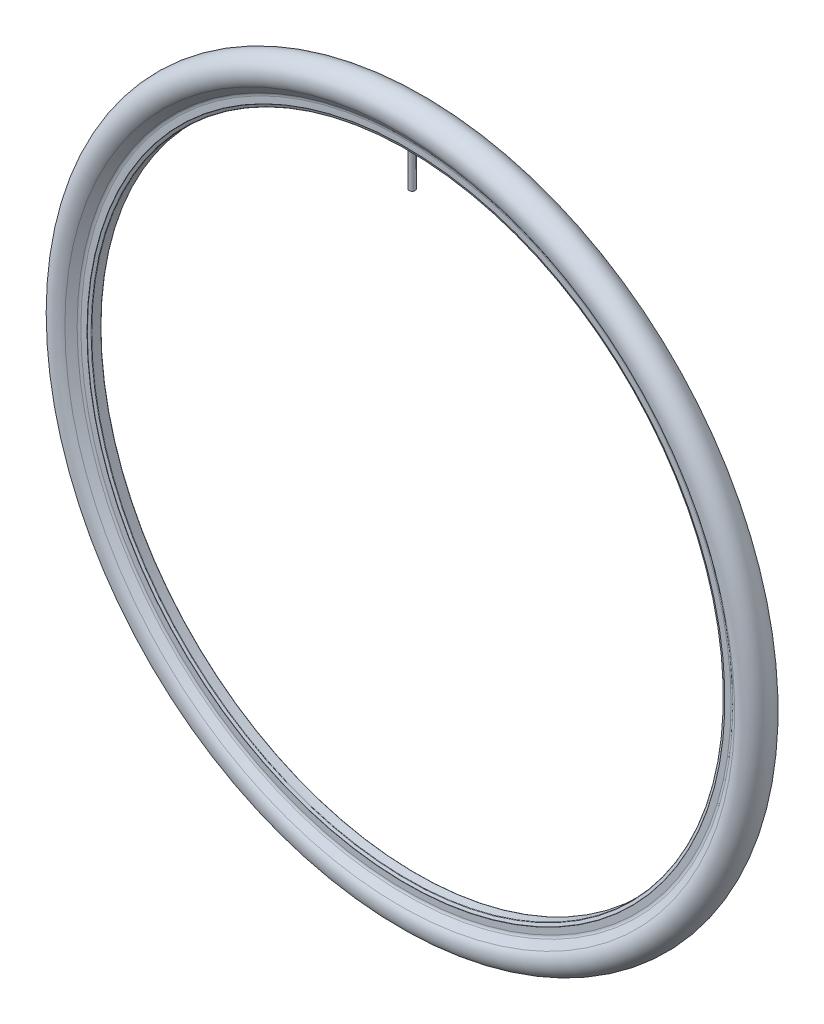
SolidWorks part; units mm, degrees
ref_plane "Plan de face" through (0, 0, 0) normal (0, 0, 1) x (1, 0, 0)
ref_plane "Plan de dessus" through (0, 0, 0) normal (0, 1, 0) x (1, 0, 0)
ref_plane "Plan de droite" through (0, 0, 0) normal (1, 0, 0) x (0, 0, -1)
sketch "Esquisse1" plane through (0, 0, 0) normal (-1, 0, 0) x (0, 0, 1)
  line L0 (-66.4925, 0) -> (62.983, 0) construction
  line L1 (0, 0) -> (0, 389.9357) construction
  line L2 (6, 316) -> (6, 310)
  line L3 (-6, 316) -> (-6, 310)
  line L4 (4.3317, 307) -> (-4.3317, 307)
  line L5 (5.8242, 309.782) -> (4.7932, 307.3077)
  line L6 (-5.8242, 309.782) -> (-4.7932, 307.3077)
  line L7 (-6.1, 319.3) -> (-11.2, 326.1)
  line L8 (-5, 316) -> (-5, 310.3623)
  line L9 (-4.024, 308.0615) -> (-4.9011, 310.1666)
  line L10 (3.9317, 308) -> (-3.9317, 308)
  line L11 (-6.9, 318.7) -> (-12, 325.5)
  line L12 (4.9011, 310.1666) -> (4.024, 308.0615)
  line L13 (5, 316) -> (5, 310.3623)
  line L14 (6.1, 319.3) -> (11.2, 326.1)
  line L15 (3.9983, 308) -> (-3.9983, 308) construction
  line L16 (4.9011, 310.1666) -> (3.9983, 308) construction
  line L19 (6.9, 318.7) -> (12, 325.5)
  line L20 (-4.9011, 310.1666) -> (-3.9983, 308) construction
  arc A0 (-6, 316) -> (-6.9, 318.7) centre (-10.5, 316) ccw
  arc A1 (6.9, 318.7) -> (6, 316) centre (10.5, 316) ccw
  arc A2 (4.7932, 307.3077) -> (4.3317, 307) centre (4.3317, 307.5) cw
  arc A3 (12, 325.5) -> (-12, 325.5) centre (0, 334.5) ccw
  arc A4 (-4.7932, 307.3077) -> (-4.3317, 307) centre (-4.3317, 307.5) ccw
  arc A5 (6, 310) -> (5.8242, 309.782) centre (6.2857, 309.5897) ccw
  arc A6 (-6, 310) -> (-5.8242, 309.782) centre (-6.2857, 309.5897) cw
  arc A7 (11.2, 326.1) -> (-11.2, 326.1) centre (0, 334.5) ccw
  arc A8 (-5, 316) -> (-6.1, 319.3) centre (-10.5, 316) ccw
  arc A9 (-5, 310.3623) -> (-4.9011, 310.1666) centre (-6.2857, 309.5897) cw
  arc A10 (4.024, 308.0615) -> (3.9317, 308) centre (3.9317, 308.1) cw
  arc A11 (-3.9317, 308) -> (-4.024, 308.0615) centre (-3.9317, 308.1) cw
  arc A12 (5, 310.3623) -> (4.9011, 310.1666) centre (6.2857, 309.5897) ccw
  arc A13 (6.1, 319.3) -> (5, 316) centre (10.5, 316) ccw
  arc A14 (-3.9983, 308) -> (-3.9983, 308) centre (-3.9983, 308) ccw construction
  arc A15 (3.9983, 308) -> (3.9983, 308) centre (3.9983, 308) cw construction
  point P12 (-6, 317.5)
  point P16 (6, 317.5)
  point P19 (4.665, 307)
  point P25 (-4.665, 307)
  dimension "D1" = 30
  dimension "D2" = 614
  dimension "D6" = 45.24
  dimension "D9" = 0.5
  dimension "D3" = 699
  dimension "D5" = 12
  dimension "D8" = 4.5
  dimension "D11" = 0.5
  dimension "D13" = 0.1
  dimension "D4" = 73.74
  dimension "D7" = 9.33
  dimension "D10" = 3
  dimension "D12" = 1
revolve "Révolution1" add sketch "Esquisse1" angle 360 about L0
sketch "Esquisse2" plane through (0, 0, 0) normal (0, 1, 0) x (1, 0, 0)
  circle A0 centre (0, 0) radius 3
  dimension "D1" = 6
extrude "Extrusion1" add sketch "Esquisse2" along normal up to next from offset 272
sketch "Esquisse3" plane through (0, 272, 0) normal (0, -1, 0) x (1, 0, 0)
  circle A0 centre (0, 0) radius 1.25
  dimension "D1" = 2.5
extrude "Enlèv. mat.-Extru.1" cut sketch "Esquisse3" against normal up to next
